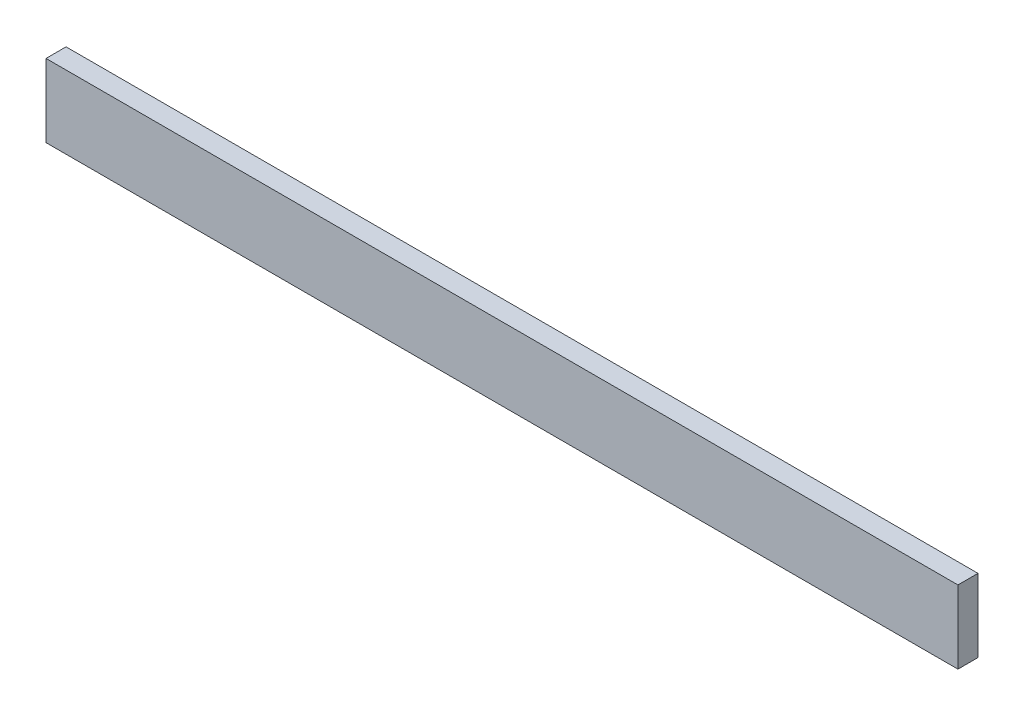
SolidWorks part; units mm, degrees
ref_plane "Face" through (0, 0, 0) normal (0, 0, 1) x (1, 0, 0)
ref_plane "Dessus" through (0, 0, 0) normal (0, 1, 0) x (1, 0, 0)
ref_plane "Droite" through (0, 0, 0) normal (1, 0, 0) x (0, 0, -1)
sketch "Esquisse1" plane through (0, 0, 0) normal (0, 0, 1) x (1, 0, 0)
  line L1 (0, 0) -> (1000, 0)
  line L2 (0, 0) -> (0, 80)
  line L3 (0, 80) -> (1000, 80)
  line L4 (1000, 0) -> (1000, 80)
  dimension "D1" = 1000
  dimension "D2" = 80
extrude "Extrusion1" add sketch "Esquisse1" along normal blind 22
